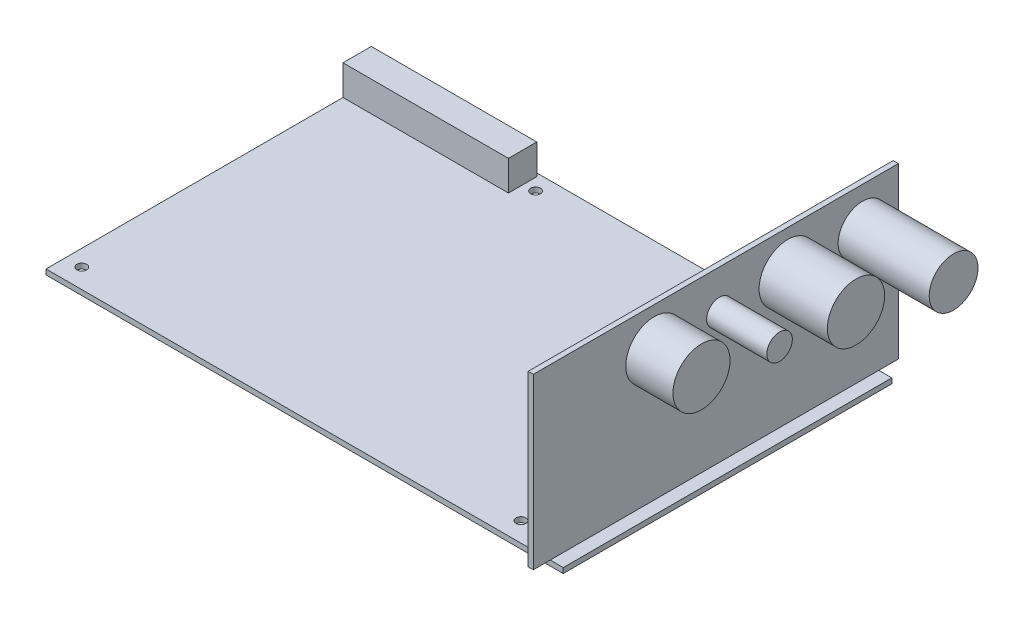
SolidWorks part; units mm, degrees
material "A-Glass Fiber"
ref_plane "Front Plane" through (0, 0, 0) normal (0, 0, 1) x (1, 0, 0)
ref_plane "Top Plane" through (0, 0, 0) normal (0, 1, 0) x (1, 0, 0)
ref_plane "Right Plane" through (0, 0, 0) normal (1, 0, 0) x (0, 0, -1)
sketch "Sketch1" plane through (0, 0, 0) normal (0, 1, 0) x (1, 0, 0)
  line L1 (-79.5, 50.5) -> (79.5, 50.5)
  line L2 (-79.5, 50.5) -> (-79.5, -50.5)
  line L3 (-79.5, -50.5) -> (79.5, -50.5)
  line L4 (79.5, 50.5) -> (79.5, -50.5)
  line L5 (-79.5, 50.5) -> (79.5, -50.5) construction
  line L6 (-79.5, -50.5) -> (79.5, 50.5) construction
  circle A0 centre (-25, 45.5) radius 1.5
  circle A1 centre (30.5, 40.5) radius 1.5
  circle A2 centre (-74.5, -44.5) radius 1.5
  circle A3 centre (60.5, -44.5) radius 1.5
  point P0 (0, 0)
  dimension "D5" = 3
  dimension "D7" = 3
  dimension "D11" = 3
  dimension "D1" = 159
  dimension "D2" = 101
  dimension "D3" = 54.5
  dimension "D4" = 5
  dimension "D6" = 110
  dimension "D8" = 10
  dimension "D9" = 6
  dimension "D10" = 5
  dimension "D12" = 135
extrude "Main Board" add sketch "Sketch1" along normal blind 1.6
sketch "Sketch2" plane through (0, 1.6, 0) normal (0, 1, 0) x (1, 0, 0)
  line L0 (-79.5, 50.5) -> (-79.5, -50.5) construction
  line L1 (-79.5, 49.5) -> (-28.63, 49.5)
  line L2 (-79.5, 49.5) -> (-79.5, 40.79)
  line L3 (-79.5, 40.79) -> (-28.63, 40.79)
  line L4 (-28.63, 49.5) -> (-28.63, 40.79)
  line L5 (79.5, 50.5) -> (-79.5, 50.5) construction
  dimension "D1" = 1
  dimension "D2" = 8.71
  dimension "D3" = 50.87
extrude "Connector" add sketch "Sketch2" along normal blind 9.24
sketch "Sketch3" plane through (0, 1.6, 0) normal (0, 1, 0) x (1, 0, 0)
  line L0 (79.5, 50.5) -> (-79.5, 50.5) construction
  line L1 (73.9, 56.5) -> (75.5, 56.5)
  line L2 (73.9, 56.5) -> (73.9, -55.7)
  line L3 (73.9, -55.7) -> (75.5, -55.7)
  line L4 (75.5, 56.5) -> (75.5, -55.7)
  line L6 (79.5, -50.5) -> (79.5, 50.5) construction
  dimension "D1" = 112.2
  dimension "D2" = 1.6
  dimension "D3" = 6
  dimension "D4" = 4
extrude "Connector Board" add sketch "Sketch3" along normal blind 52.04
sketch "Sketch4" plane through (75.5, 0, 0) normal (1, 0, 0) x (0, 0, -1)
  line L0 (-55.7, 53.64) -> (56.5, 53.64) construction
  line L1 (56.5, 53.64) -> (56.5, 1.6) construction
  circle A0 centre (45.5, 41.64) radius 7.5
  dimension "D3" = 15
  dimension "D1" = 12
  dimension "D2" = 11
extrude "CAN Connector" add sketch "Sketch4" along normal blind 28
sketch "Sketch5" plane through (75.5, 0, 0) normal (1, 0, 0) x (0, 0, -1)
  line L0 (56.5, 53.64) -> (56.5, 1.6) construction
  line L2 (45.5, 41.64) -> (22.5, 41.64) construction
  circle A0 centre (22.5, 41.64) radius 8.8
  dimension "D1" = 17.6
  dimension "D2" = 34
extrude "Main LV Connector" add sketch "Sketch5" along normal blind 21
sketch "Sketch6" plane through (75.5, 0, 0) normal (1, 0, 0) x (0, 0, -1)
  line L0 (22.5, 41.64) -> (1.5, 41.64) construction
  line L2 (56.5, 53.64) -> (56.5, 1.6) construction
  circle A0 centre (1.5, 41.64) radius 3.93
  circle A1 centre (22.5, 41.64) radius 8.8 construction
  dimension "D1" = 7.86
  dimension "D2" = 55
extrude "Serial Connector" add sketch "Sketch6" along normal blind 18.5
sketch "Sketch7" plane through (75.5, 0, 0) normal (1, 0, 0) x (0, 0, -1)
  line L0 (-18.5, 41.64) -> (1.5, 41.64) construction
  line L1 (56.5, 53.64) -> (56.5, 1.6) construction
  circle A0 centre (-18.5, 41.64) radius 8.775
  circle A1 centre (1.5, 41.64) radius 3.93 construction
  dimension "D2" = 17.55
  dimension "D1" = 75
extrude "Feedback Connector" add sketch "Sketch7" along normal blind 14.5
